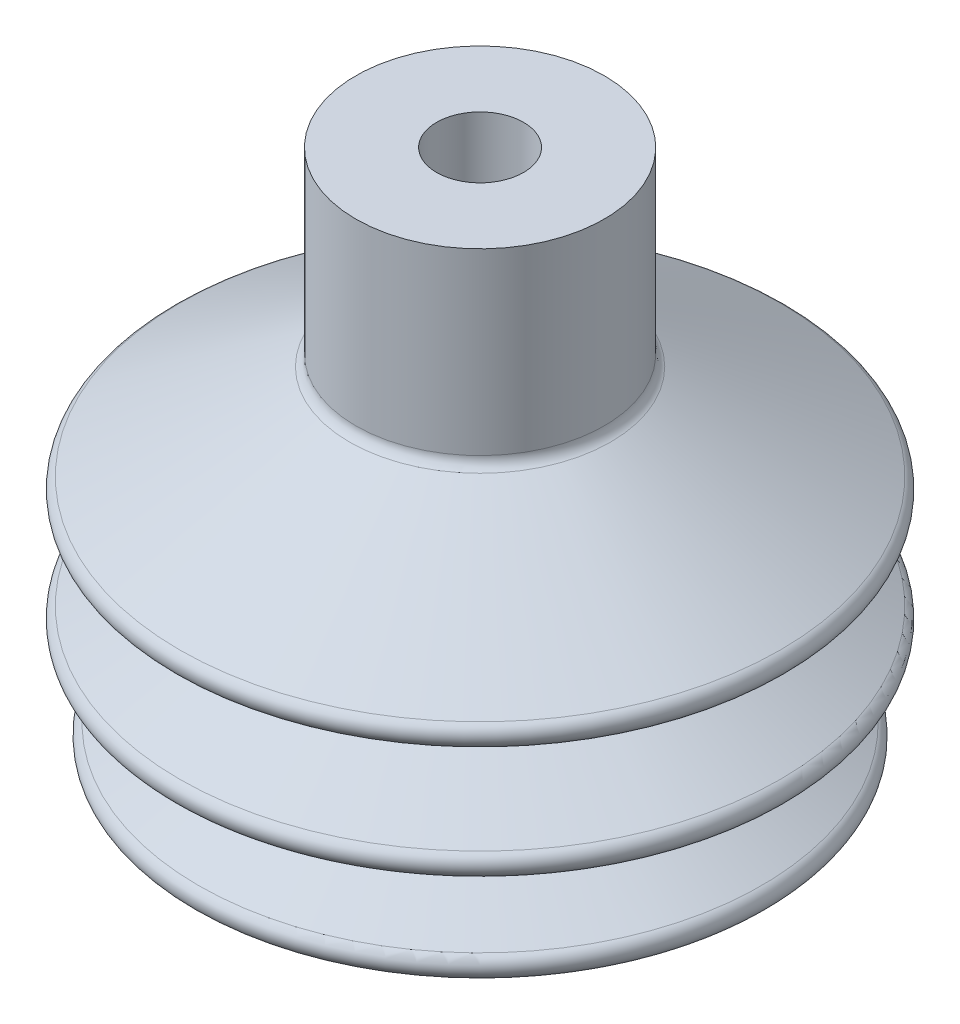
SolidWorks part; units mm, degrees
ref_plane "前视基准面" through (0, 0, 0) normal (0, 0, 1) x (1, 0, 0)
ref_plane "上视基准面" through (0, 0, 0) normal (0, 1, 0) x (1, 0, 0)
ref_plane "右视基准面" through (0, 0, 0) normal (1, 0, 0) x (0, 0, -1)
sketch "草图1" plane through (0, 0, 0) normal (0, 1, 0) x (1, 0, 0)
  circle A0 centre (0, 0) radius 10
  circle A1 centre (0, 0) radius 3.5
  dimension "D1" = 20
  dimension "D2" = 7
extrude "凸台-拉伸1" add sketch "草图1" along normal blind 15
sketch "草图2" plane through (0, 0, 0) normal (0, 0, 1) x (1, 0, 0)
  line L0 (0, 0) -> (0, 19.3092)
  line L1 (-10, 0) -> (10, 0) construction
sketch "草图3" plane through (0, 0, 0) normal (0, 0, 1) x (1, 0, 0)
  line L0 (10, 0) -> (26, -8.9661)
  line L1 (26, -8.9661) -> (16.6245, -12.7292)
  line L2 (16.6245, -12.7292) -> (26, -17.983)
  line L3 (26, -17.983) -> (16.6245, -21.7462)
  line L4 (16.6245, -21.7462) -> (26, -27)
  line L5 (26, -27) -> (21.9088, -27)
  line L6 (21.9088, -27) -> (12, -21.4473)
  line L7 (12, -21.4473) -> (21.3755, -17.6842)
  line L8 (21.3755, -17.6842) -> (12, -12.4303)
  line L9 (12, -12.4303) -> (21.3755, -8.6672)
  line L10 (21.3755, -8.6672) -> (5.9088, 0)
  line L11 (-10, 0) -> (10, 0) construction
  line L12 (5.9088, 0) -> (10, 0)
  line L13 (0, 0) -> (0, 19.3092) construction
  point P9 (11.2642, -20.0027)
  point P16 (27.3656, -23.1648)
  point P17 (27.3656, -32.7516)
  point P18 (0, 0)
  point P19 (0, 0)
  point P20 (10.0429, -16.7402)
  point P21 (27.7609, -8.8888)
  point P22 (14.0445, -13.149)
  dimension "D1" = 2
  dimension "D2" = 2
  dimension "D3" = 2
  dimension "D4" = 2
  dimension "D5" = 2
  dimension "D6" = 27
  dimension "D7" = 12
  dimension "D8" = 26
revolve "旋转1" add sketch "草图3" angle 360 about L0
fillet "圆角1" radius 1 4 edges at (0, 0, -10) (0, -27, -26) (0, -17.983, -26) (0, -8.9661, -26)
